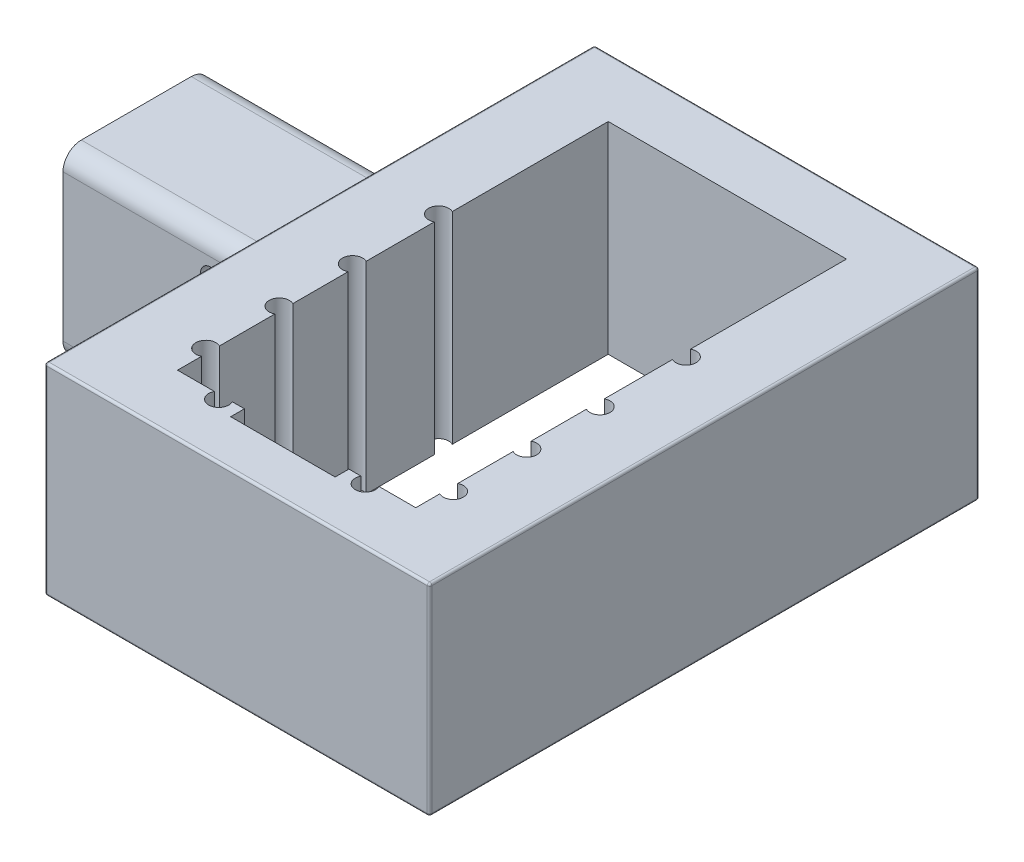
SolidWorks part; units mm, degrees
material "ABS PC"
ref_plane "Front Plane" through (0, 0, 0) normal (0, 0, 1) x (1, 0, 0)
ref_plane "Top Plane" through (0, 0, 0) normal (0, 1, 0) x (1, 0, 0)
ref_plane "Right Plane" through (0, 0, 0) normal (1, 0, 0) x (0, 0, -1)
sketch "Sketch1" plane through (0, 0, 0) normal (1, 0, 0) x (0, 0, -1)
  line L1 (6, -10) -> (-6, -10)
  line L2 (8, -8) -> (8, 8)
  line L3 (6, 10) -> (-6, 10)
  line L4 (-8, -8) -> (-8, 8)
  line L5 (8, -10) -> (-8, 10) construction
  line L6 (8, 10) -> (-8, -10) construction
  line L7 (5.75, -7.5) -> (-5.75, -7.5)
  line L8 (6, -7.25) -> (6, 7.25)
  line L9 (5.75, 7.5) -> (-5.75, 7.5)
  line L10 (-6, -7.25) -> (-6, 7.25)
  line L11 (6, -7.5) -> (-6, 7.5) construction
  line L12 (6, 7.5) -> (-6, -7.5) construction
  arc A0 (-6, 10) -> (-8, 8) centre (-6, 8) ccw
  arc A1 (6, 10) -> (8, 8) centre (6, 8) cw
  arc A2 (6, -10) -> (8, -8) centre (6, -8) ccw
  arc A3 (-6, -10) -> (-8, -8) centre (-6, -8) cw
  arc A4 (-6, -10) -> (-8, -8) centre (-6, -8) cw
  arc A5 (-5.75, 7.5) -> (-6, 7.25) centre (-5.75, 7.25) ccw
  arc A6 (6, 7.25) -> (5.75, 7.5) centre (5.75, 7.25) ccw
  arc A7 (5.75, -7.5) -> (6, -7.25) centre (5.75, -7.25) ccw
  arc A8 (-6, -7.25) -> (-5.75, -7.5) centre (-5.75, -7.25) ccw
  point P0 (0, 0)
  point P21 (0, 0)
  point P41 (0, 0)
  dimension "D3" = 2
  dimension "D4" = 2
  dimension "D5" = 2
  dimension "D6" = 2
  dimension "D7" = 2
  dimension "D10" = 0.25
  dimension "D11" = 0.25
  dimension "D12" = 0.25
  dimension "D13" = 0.25
  dimension "D1" = 20
  dimension "D2" = 16
  dimension "D8" = 15
  dimension "D9" = 12
sketch "Sketch3" plane through (0, 0, 0) normal (1, 0, 0) x (0, 0, -1)
  line L2 (8.0219, 0) -> (-7.9955, 0) construction
  point P0 (8.0219, 0)
  point P1 (-7.9955, 0)
ref_plane "Plane3" through (0, 0, 8) normal (0, 0, 1) x (1, 0, 0)
sketch "Sketch8" plane through (0, 0, 8) normal (0, 0, 1) x (1, 0, 0)
  line L1 (0, 0) -> (0, 5.9602) construction
  line L2 (0, 0) -> (0, -6.0008) construction
  circle A0 centre (0, 5.9602) radius 1.0896
  circle A1 centre (0, -6.0008) radius 1.0826
ref_plane "Plane4" through (0, 0, -8) normal (0, 0, 1) x (1, 0, 0)
sketch "Sketch9" plane through (0, 0, -8) normal (0, 0, 1) x (1, 0, 0)
  line L0 (0, 0) -> (0, 6.0252) construction
  line L1 (0, 0) -> (0, -5.9783) construction
  circle A0 centre (0, 6.0252) radius 1.0875
  circle A1 centre (0.2177, -5.9783) radius 1.097
extrude "Boss-Extrude3" add sketch "Sketch1" along normal blind 3.9 and the other way blind 16.1 contours A3 L1 A2 L2 A1 L3 A0 L4 A8 L10 A5 L9 A6 L8 A7 L7
extrude "Cut-Extrude2" cut sketch "Sketch8" against normal blind 23.9 contours A0
extrude "Cut-Extrude3" cut sketch "Sketch9" along normal blind 23.9 contours A1
ref_plane "Plane6" through (3.9, 0, 0) normal (1, 0, 0) x (0, 0, -1)
sketch "Sketch14" plane through (3.9, 0, 0) normal (1, 0, 0) x (0, 0, -1)
  line L1 (30, -11) -> (-30, -11)
  line L2 (30, -11) -> (30, 11)
  line L3 (30, 11) -> (-30, 11)
  line L4 (-30, -11) -> (-30, 11)
  line L5 (30, -11) -> (-30, 11) construction
  line L6 (30, 11) -> (-30, -11) construction
  point P0 (0, 0)
  dimension "D1" = 22
  dimension "D2" = 60
extrude "Boss-Extrude4" add sketch "Sketch14" along normal blind 42 contours L3 L4 L1 L2
ref_plane "Plane10" through (0, 0, 0) normal (0, 1, 0) x (1, 0, 0)
sketch "Sketch19" plane through (0, 0, 0) normal (0, 1, 0) x (1, 0, 0)
  line L0 (11.9, -23.5) -> (19.2, -23.5)
  line L1 (37.9, -23.5) -> (30.6, -23.5)
  line L2 (19.2, -23.5) -> (19.2, -25)
  line L3 (30.6, -23.5) -> (30.6, -25)
  line L6 (37.9, -23.5) -> (37.9, 23.5)
  line L7 (37.9, 23.5) -> (11.9, 23.5)
  line L8 (11.9, -23.5) -> (11.9, 23.5)
  line L9 (37.9, -23.5) -> (11.9, 23.5) construction
  line L10 (37.9, 23.5) -> (11.9, -23.5) construction
  line L11 (19.2, -25) -> (30.6, -25)
  point P0 (24.9, 0)
  point P8 (24.9, -23.5)
  point P12 (24.9, 0)
  dimension "D1" = 47
  dimension "D2" = 26
extrude "Cut-Extrude4" cut sketch "Sketch19" along normal blind 22 and the other way blind 25
fillet "Fillet5" radius 0.25 20 edges at (45.9, -11, 0) (45.9, 11, 0) (24.9, -11, -30) (45.9, 0, -30) (24.9, 11, -30) (3.9, 9.4142, 7.4142) (3.9, 10, 0) (3.9, 9.4142, -7.4142) (3.9, 0, -8) (3.9, -9.4142, -7.4142) (3.9, -10, 0) (3.9, -9.4142, 7.4142) (3.9, 0, 8) (3.9, 11, 0) (3.9, -11, 0) (3.9, 0, -30) (24.9, 11, 30) (45.9, 0, 30) (24.9, -11, 30) (3.9, 0, 30)
ref_plane "Plane11" through (0, 11, 0) normal (0, 1, 0) x (1, 0, 0)
sketch "Sketch20" plane through (0, 11, 0) normal (0, 1, 0) x (1, 0, 0)
  line L0 (24.9, -29.75) -> (24.9, 29.75) construction
  line L1 (4.15, -29.75) -> (45.65, -29.75) construction
  line L2 (45.65, 29.75) -> (4.15, 29.75) construction
  circle A0 centre (11.4, 5.5) radius 1.1
  circle A1 centre (11.4, -3.9) radius 1.1
  circle A2 centre (11.4, -11.9) radius 1.1
  circle A3 centre (11.4, -19.9) radius 1.1
  circle A4 centre (38.4, -19.9) radius 1.1
  circle A5 centre (38.4, -11.9) radius 1.1
  circle A6 centre (38.4, -3.9) radius 1.1
  circle A7 centre (38.4, 5.5) radius 1.1
  point P6 (11.9, 5.5)
  point P10 (11.9, -3.9)
  point P11 (11.9, -11.9)
  point P12 (11.9, -19.9)
  point P13 (11.4, 5.5)
  point P14 (11.4, -3.9)
  point P15 (11.4, -11.9)
  point P16 (11.4, -19.9)
extrude "Cut-Extrude6" cut sketch "Sketch20" against normal blind 110
sketch "Sketch23" plane through (0, 11, 0) normal (0, 1, 0) x (1, 0, 0)
  line L0 (16.9, -23.5) -> (16.9, -24) construction
  line L3 (32.9, -23.5) -> (32.9, -24) construction
  circle A0 centre (16.9, -24) radius 1.1
  circle A1 centre (32.9, -24) radius 1.1
  point P13 (16.9, -23.5)
  point P14 (32.9, -23.5)
extrude "Cut-Extrude7" cut sketch "Sketch23" against normal blind 110
ref_plane "Plane12" through (45.9, 10.75, 29.75) normal (0, 0, 1) x (1, 0, 0)
